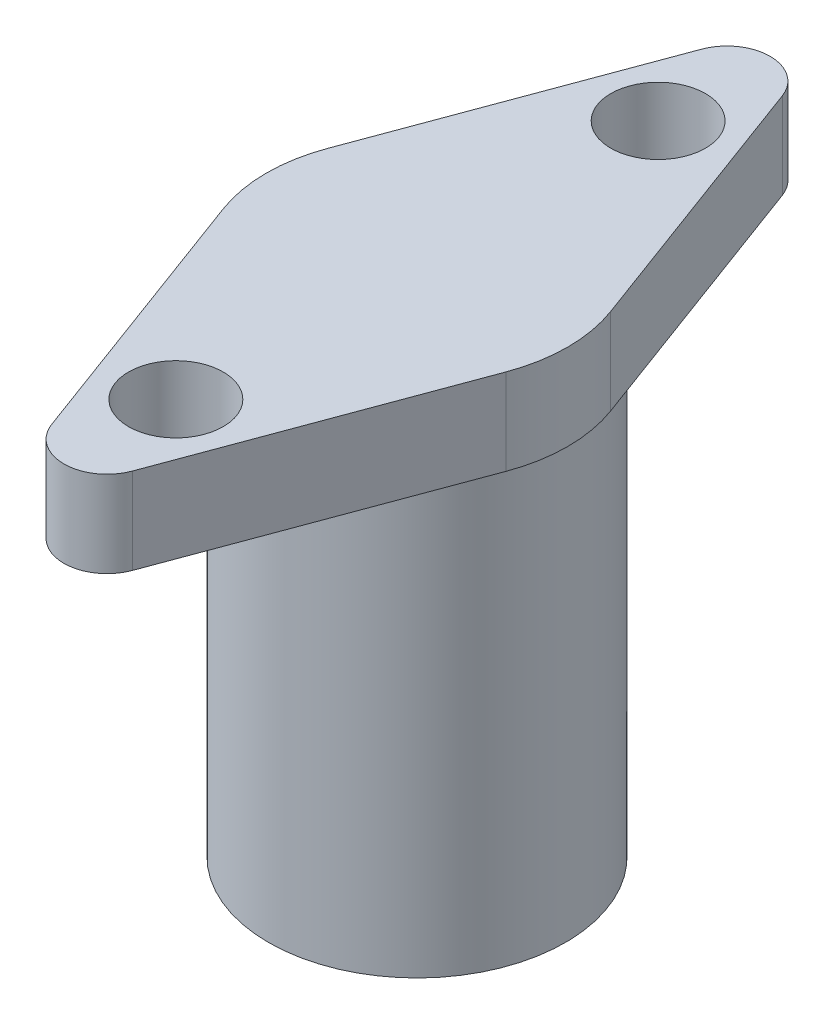
SolidWorks part; units mm, degrees
ref_plane "Front Plane" through (0, 0, 0) normal (0, 0, 1) x (1, 0, 0)
ref_plane "Top Plane" through (0, 0, 0) normal (0, 1, 0) x (1, 0, 0)
ref_plane "Right Plane" through (0, 0, 0) normal (1, 0, 0) x (0, 0, -1)
sketch "Sketch1" plane through (0, 0, 0) normal (0, 1, 0) x (1, 0, 0)
  circle A0 centre (0, 0) radius 2.1
  circle A1 centre (0, 0) radius 3.45
  dimension "D1" = 4.2
  dimension "D2" = 6.9
extrude "Boss-Extrude1" add sketch "Sketch1" along normal blind 10
sketch "Sketch2" plane through (0, 10, 0) normal (0, 1, 0) x (1, 0, 0)
  line L0 (-3.2823, 1.2152) -> (-0.9378, 7.5475)
  line L1 (0.9378, 7.5475) -> (3.2823, 1.2152)
  line L2 (3.5, 0) -> (-3.5, 0) construction
  line L3 (-3.2823, -1.2152) -> (-0.9378, -7.5475)
  line L4 (0.9378, -7.5475) -> (3.2823, -1.2152)
  line L5 (0, 7.2003) -> (0, -7.2003) construction
  arc A0 (-3.2823, 1.2152) -> (-3.2823, -1.2152) centre (0, 0) ccw
  arc A1 (-0.9378, -7.5475) -> (0.9378, -7.5475) centre (0, -7.2003) ccw
  arc A2 (-0.9378, 7.5475) -> (0.9378, 7.5475) centre (0, 7.2003) cw
  arc A3 (3.2823, -1.2152) -> (3.2823, 1.2152) centre (0, 0) ccw
  circle A6 centre (0, -5.6) radius 1.1
  circle A7 centre (0, 5.6) radius 1.1
  point P13 (0, -10.0804)
  point P16 (0, 10.0804)
  dimension "D1" = 1
  dimension "D2" = 3.5
  dimension "D4" = 5.6
  dimension "D5" = 2.2
  dimension "D3" = 7.2003
extrude "Boss-Extrude2" add sketch "Sketch2" along normal blind 2
